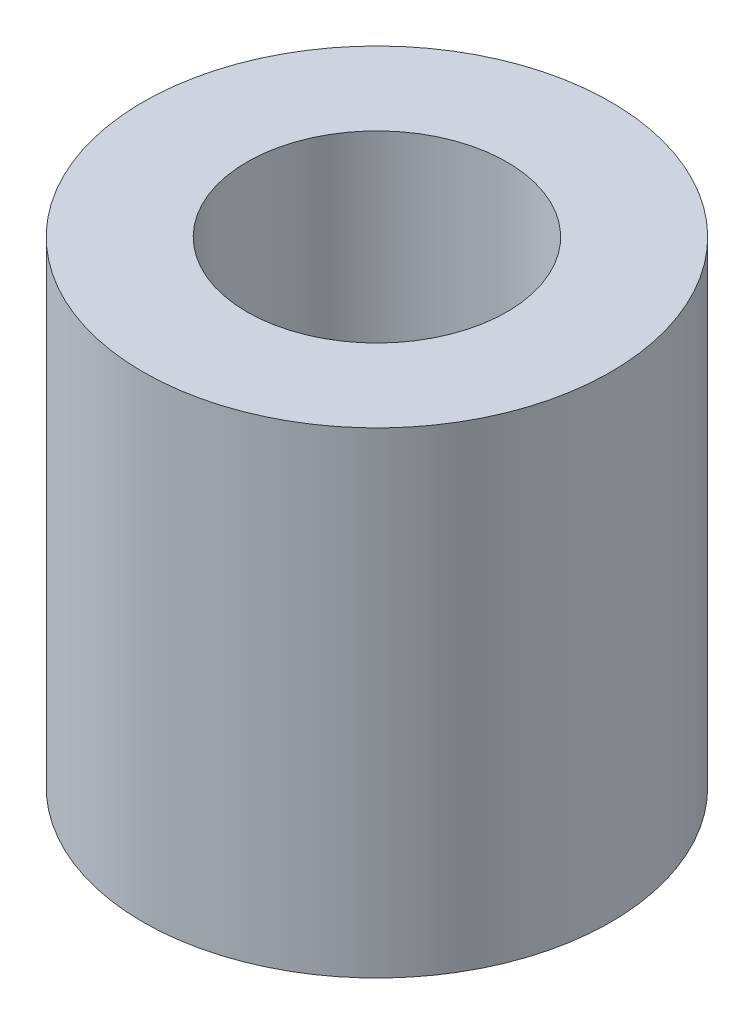
SolidWorks part; units mm, degrees
ref_plane "Front Plane" through (0, 0, 0) normal (0, 0, 1) x (1, 0, 0)
ref_plane "Top Plane" through (0, 0, 0) normal (0, 1, 0) x (1, 0, 0)
ref_plane "Right Plane" through (0, 0, 0) normal (1, 0, 0) x (0, 0, -1)
sketch "Sketch2" plane through (0, 0, 0) normal (0, 1, 0) x (1, 0, 0)
  circle A0 centre (0, 0) radius 2.7
  circle A1 centre (0, 0) radius 1.5
  dimension "D1" = 5.4
  dimension "D2" = 3
extrude "Boss-Extrude1" add sketch "Sketch2" along normal blind 5.5
